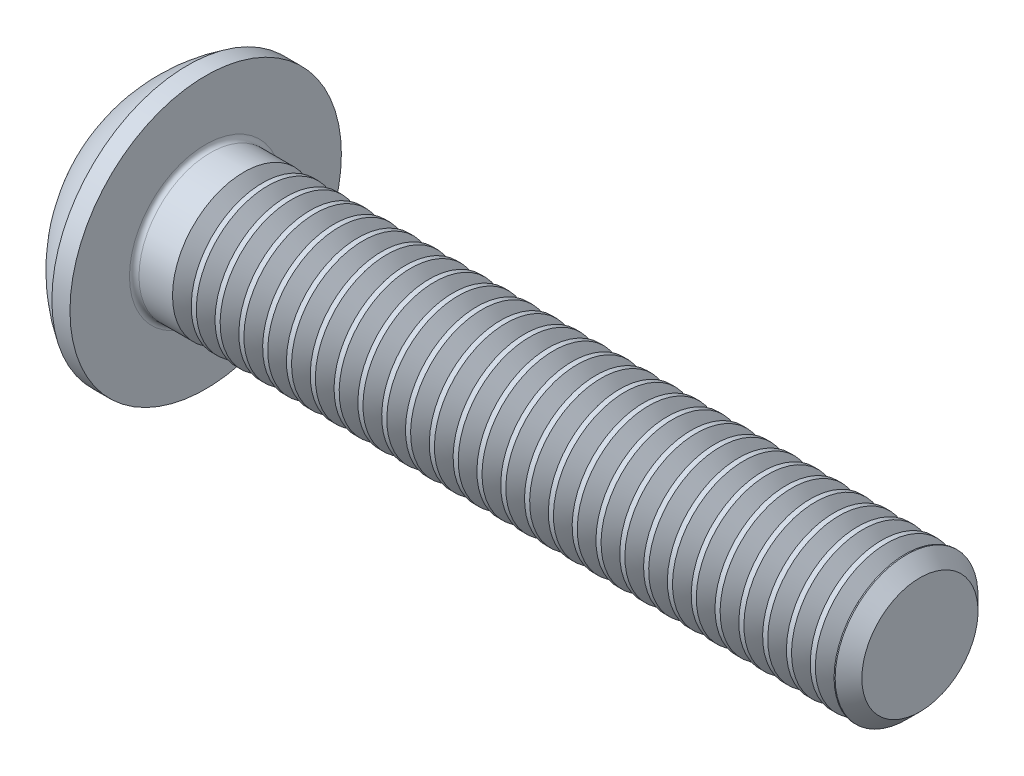
SolidWorks part; units mm, degrees
ref_plane "Plane1" through (0, 0, 0) normal (0, 0, 1) x (1, 0, 0)
ref_plane "Plane2" through (0, 0, 0) normal (0, 1, 0) x (1, 0, 0)
ref_plane "Plane3" through (0, 0, 0) normal (1, 0, 0) x (0, 0, -1)
sketch "BodySke" plane through (0, 0, 0) normal (0, 0, 1) x (1, 0, 0)
  line L0 (16.65, 0) -> (16.65, 1.2195)
  line L1 (16.3695, 1.5) -> (1.65, 1.5)
  line L2 (1.65, 1.5) -> (1.65, 2.85)
  line L3 (1.65, 2.85) -> (1.27, 2.85)
  line L4 (0, 0) -> (101.6, 0) construction
  line L5 (1.65, -2.85) -> (1.27, -2.85) construction
  line L6 (55.6768, -1.5) -> (1.65, -1.5) construction
  line L7 (16.65, 0) -> (0, 0)
  line L8 (0, 1.425) -> (0, -1.425) construction
  line L9 (0, 0) -> (0, 1.425)
  line L10 (16.65, 1.2195) -> (16.3695, 1.5)
  line L11 (16.65, -1.2195) -> (16.3695, -1.5) construction
  line L12 (2.15, 9.525) -> (2.15, -1.5) construction
  line L13 (1.65, 9.525) -> (1.65, -1.5) construction
  arc A1 (0, 1.425) -> (1.27, 2.85) centre (3.0334, 0) cw
  dimension "Diameter" = 3
  dimension "Length" = 15
  dimension "Head_dia" = 5.7
  dimension "D1" = 2.85
  dimension "Head_ht" = 1.65
  dimension "Head_side_ht" = 0.38
  dimension "Minor_dia" = 2.439
  dimension "Body_ch_ang" = 45
  dimension "Advance" = 0.5
  dimension "Thread_nom" = 15
revolve "BaseBody" add sketch "BodySke" angle 360 about L4
cosmetic thread "ThreadCosmetic" [suppressed] parameters "Thread_length"=14, "Thread_minor"=2.439
fillet "Fillet1" radius 0.1 1 edges at (1.65, 0, 1.5)
sketch "Sketch2" plane through (0, 0, 0) normal (0, 0, 1) x (1, 0, 0)
  line L0 (0, 1) -> (1.04, 1)
  line L1 (1.04, 1) -> (1.6174, 0)
  line L3 (1.6174, 0) -> (0, 0)
  line L4 (0, 0) -> (0, 1)
  line L5 (0, -1) -> (1.04, -1) construction
  line L6 (0, 0) -> (47.625, 0) construction
  dimension "D2" = 60
  dimension "PreBroach_depth" = 1.04
  dimension "PreBroach_dia" = 2
revolve "PreBroach" cut sketch "Sketch2" angle 360 about L6
sketch "Sketch3" plane through (0, 0, 0) normal (1, 0, 0) x (0, 0, -1)
  line L0 (-1, -0.5774) -> (-1, 0.5774)
  line L1 (-1, 0.5774) -> (0, 1.1547)
  line L2 (0, 1.1547) -> (1, 0.5774)
  line L3 (1, 0.5774) -> (1, -0.5774)
  line L4 (1, -0.5774) -> (0, -1.1547)
  line L5 (0, -1.1547) -> (-1, -0.5774)
  dimension "Hex_size" = 2
  dimension "D3" = 2
  dimension "D1" = 1
  dimension "D2" = 1
extrude "Hex" cut sketch "Sketch3" along normal blind 1.04
sketch "ThdSchSke" plane through (0, 0, 0) normal (0, 0, 1) x (1, 0, 0)
  line L0 (2.65, -1.2195) -> (2.4536, -1.5)
  line L1 (2.65, -1.2195) -> (2.8464, -1.5)
  line L2 (2.8464, -1.5) -> (2.8464, -1.875)
  line L3 (-3.175, 0) -> (5.1513, 0) construction
  line L5 (2.8464, -1.875) -> (2.4536, -1.875)
  line L6 (2.4536, -1.875) -> (2.4536, -1.5)
  dimension "Diameter" = 3
  dimension "Thread_minor" = 2.439
  dimension "SideAngle" = 55
  dimension "VeeAngle" = 70
  dimension "Overcut" = 3.75
  dimension "Start" = 2.65
revolve "ThreadSchematic" cut sketch "ThdSchSke" angle 360 about L3
pattern_linear "ThdSchPat" count 28 spacing 0.5 along (1, 0, 0) of "ThreadSchematic"
equation "\"D1@BodySke\" = \"Head_dia@BodySke\" * .5"
equation "\"Thread_minor@ThreadCosmetic\" = \"Minor_dia@BodySke\""
equation "\"D1@Sketch3\" = \"Hex_size@Sketch3\" / 2"
equation "\"D2@Sketch3\" = \"D1@Sketch3\""
equation "\"D3@Sketch3\" = \"Hex_size@Sketch3\""
equation "\"Thread_length@ThreadCosmetic\" = ((sgn( (\"Length@BodySke\" - \"Advance@BodySke\" * 2.0) - \"Thread_nom@BodySke\" )-1)*( (\"Length@BodySke\" - \"Advance@BodySke\" * 2.0) - \"Thread_nom@BodySke\" ))/-2+ \"Thread_nom@BodySke\""
equation "\"Thread_minor@ThdSchSke\" = \"Minor_dia@BodySke\""
equation "\"Diameter@ThdSchSke\" = \"Diameter@BodySke\""
equation "\"Overcut@ThdSchSke\" = \"Diameter@BodySke\" * 1.25"
equation "\"Start@ThdSchSke\" = \"Head_ht@BodySke\" + \"Length@BodySke\" - \"Thread_length@ThreadCosmetic\"  '---Non-countersunk---"
equation "\"Num_threads@ThdSchPat\" = int( \"Thread_length@ThreadCosmetic\" / \"Advance@BodySke\" + 0.999 )  + 1"
equation "\"Advance@ThdSchPat\" = \"Thread_length@ThreadCosmetic\" /  (\"Num_threads@ThdSchPat\" - 1) 'relax it"
equation "\"Num_threads@ThdSchPat\" = \"Num_threads@ThdSchPat\" - sgn( \"Num_threads@ThdSchPat\" - 1) '---chamfered tips only---"
equation "\"Thread_nom@BodySke\"=\"Length@BodySke\""
